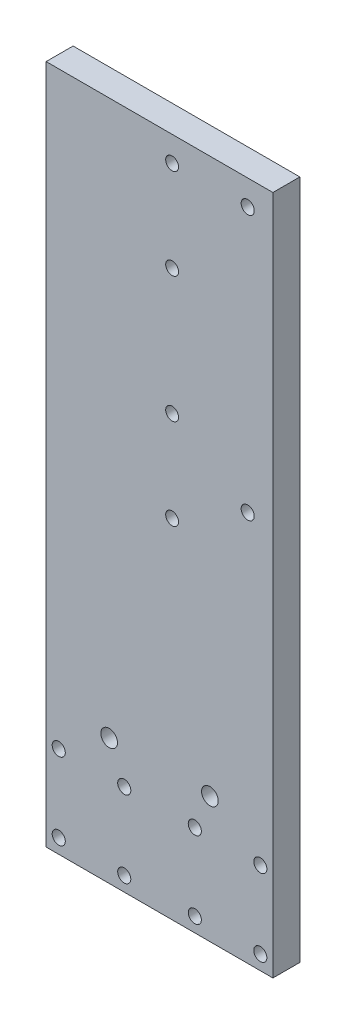
SolidWorks part; units mm, degrees
ref_plane "Plano frontal" through (0, 0, 0) normal (0, 0, 1) x (1, 0, 0)
ref_plane "Plano superior" through (0, 0, 0) normal (0, 1, 0) x (1, 0, 0)
ref_plane "Plano direito" through (0, 0, 0) normal (1, 0, 0) x (0, 0, -1)
sketch "Esboço1" plane through (0, 0, 0) normal (0, 0, 1) x (1, 0, 0)
  line L1 (45, -135) -> (-45, -135)
  line L2 (45, -135) -> (45, 135)
  line L3 (45, 135) -> (-45, 135)
  line L4 (-45, -135) -> (-45, 135)
  line L5 (45, -135) -> (-45, 135) construction
  line L6 (45, 135) -> (-45, -135) construction
  point P0 (0, 0)
  dimension "D1" = 270
  dimension "D2" = 90
extrude "Ressalto-extrusão1" add sketch "Esboço1" along normal blind 10.7
hole_wizard "Furo roscado para conduíte de M5x0.81" positions "Esboço8" profile "Esboço7" tap size "M5x0.8" standard "Helicoil® Metric" end condition through all
sketch "Esboço8" plane through (0, 0, 0) normal (0, 0, -1) x (-1, 0, 0)
  line L0 (-45, -135) -> (-45, 135) construction
  line L1 (45, -135) -> (-45, -135) construction
  line L2 (0, -143.4469) -> (0, -68.9087) construction
  point P0 (-40, -98.75)
  point P2 (-40, -129.25)
  point P4 (-14, -129.25)
  point P6 (-14, -98.75)
  point P24 (14, -98.75)
  point P25 (14, -129.25)
  point P26 (40, -129.25)
  point P27 (40, -98.75)
  dimension "D1" = 5
  dimension "D2" = 26
  dimension "D3" = 30.5
  dimension "D4" = 5.75
sketch "Esboço7" plane through (40, -98.75, 0) normal (1, 0, 0) x (0, 1, 0)
  line L0 (0, 0) -> (0, 10.7)
  line L1 (0, 10.7) -> (2.6, 10.7)
  line L2 (2.6, 10.7) -> (2.6, 0)
  line L5 (2.6, 0) -> (0, 0)
  line L11 (0, -6.35) -> (0, 107.95) construction
  dimension "Thru Tap Drill Dia." = 5.2
  dimension "Thru Tap Drill Depth" = 10.7
cosmetic thread "Rosca de furo1" parameters "D1"=10.7, "D2"=6.145
cosmetic thread "Rosca de furo2" parameters "D1"=10.7, "D2"=6.145
cosmetic thread "Rosca de furo3" parameters "D1"=10.7, "D2"=6.145
cosmetic thread "Rosca de furo4" parameters "D1"=10.7, "D2"=6.145
cosmetic thread "Rosca de furo5" parameters "D1"=10.7, "D2"=6.145
cosmetic thread "Rosca de furo6" parameters "D1"=10.7, "D2"=6.145
cosmetic thread "Rosca de furo7" parameters "D1"=10.7, "D2"=6.145
cosmetic thread "Rosca de furo8" parameters "D1"=10.7, "D2"=6.145
hole_wizard "Furo roscado para conduíte de 1/4-281" positions "Esboço9" profile "Esboço10" tap size "1/4-28" standard "Helicoil® Inch" end condition through all
sketch "Esboço9" plane through (0, 0, 0) normal (0, 0, -1) x (-1, 0, 0)
  line L0 (-45, -135) -> (-45, 135) construction
  line L1 (0, -143.4941) -> (0, -53.6494) construction
  circle A0 centre (-40, -98.75) radius 2.6 construction
  point P0 (-20, -85)
  point P12 (20, -85)
  dimension "D1" = 25
  dimension "D2" = 13.75
sketch "Esboço10" plane through (20, -85, 0) normal (1, 0, 0) x (0, 1, 0)
  line L0 (0, 0) -> (0, 10.7)
  line L1 (0, 10.7) -> (3.3147, 10.7)
  line L2 (3.3147, 10.7) -> (3.3147, 0)
  line L5 (3.3147, 0) -> (0, 0)
  line L11 (0, -6.35) -> (0, 107.95) construction
  dimension "Thru Tap Drill Dia." = 6.6294
  dimension "Thru Tap Drill Depth" = 10.7
cosmetic thread "Rosca de furo9" parameters "D1"=15, "D2"=7.6073
cosmetic thread "Rosca de furo10" parameters "D1"=15, "D2"=7.6073
hole_wizard "Furo roscado para conduíte de M5x0.82" positions "Esboço11" profile "Esboço12" tap size "M5x0.8" standard "Helicoil® Metric" end condition through all
sketch "Esboço11" plane through (0, 0, 0) normal (0, 0, -1) x (-1, 0, 0)
  line L0 (-45, -135) -> (-45, 135) construction
  line L1 (-45, 135) -> (45, 135) construction
  point P15 (-35, 125)
  point P17 (-35, 20)
  point P24 (0, 0)
  dimension "D1" = 10
  dimension "D2" = 10
  dimension "D3" = 105
sketch "Esboço12" plane through (35, 125, 0) normal (1, 0, 0) x (0, 1, 0)
  line L0 (0, 0) -> (0, 10.7)
  line L1 (0, 10.7) -> (2.6, 10.7)
  line L2 (2.6, 10.7) -> (2.6, 0)
  line L5 (2.6, 0) -> (0, 0)
  line L11 (0, -6.35) -> (0, 107.95) construction
  dimension "Thru Tap Drill Dia." = 5.2
  dimension "Thru Tap Drill Depth" = 10.7
cosmetic thread "Rosca de furo12" parameters "D1"=15, "D2"=6.145
cosmetic thread "Rosca de furo17" parameters "D1"=15, "D2"=6.145
hole_wizard "Furo roscado para conduíte de #10-321" positions "Esboço13" profile "Esboço14" tap size "#10-32" standard "Helicoil® Inch" end condition through all
sketch "Esboço13" plane through (0, 0, 0) normal (0, 0, -1) x (-1, 0, 0)
  line L0 (45, 135) -> (45, -135) construction
  line L1 (-45, 135) -> (45, 135) construction
  point P0 (-5, 125)
  point P2 (-5, 89)
  point P4 (-5, 39)
  point P6 (-5, 3)
  dimension "D1" = 50
  dimension "D2" = 10
  dimension "D3" = 36
  dimension "D4" = 50
  dimension "D5" = 36
sketch "Esboço14" plane through (5, 125, 0) normal (1, 0, 0) x (0, 1, 0)
  line L0 (0, 0) -> (0, 10.7)
  line L1 (0, 10.7) -> (2.5527, 10.7)
  line L2 (2.5527, 10.7) -> (2.5527, 0)
  line L5 (2.5527, 0) -> (0, 0)
  line L11 (0, -6.35) -> (0, 107.95) construction
  dimension "Thru Tap Drill Dia." = 5.1054
  dimension "Thru Tap Drill Depth" = 10.7
cosmetic thread "Rosca de furo13" parameters "D1"=15, "D2"=5.936
cosmetic thread "Rosca de furo14" parameters "D1"=15, "D2"=5.936
cosmetic thread "Rosca de furo15" parameters "D1"=15, "D2"=5.936
cosmetic thread "Rosca de furo16" parameters "D1"=15, "D2"=5.936
sketch "Esboço16" plane through (0, 0, 0) normal (0, 0, -1) x (-1, 0, 0)
  line L0 (45, 135) -> (45, -135) construction
  circle A0 centre (-4, 64) radius 11
  circle A1 centre (-5, 89) radius 2.5527 construction
  dimension "D1" = 22
  dimension "D2" = 49
  dimension "D3" = 25
extrude "Corte-extrusão1" cut sketch "Esboço16" against normal blind 7
